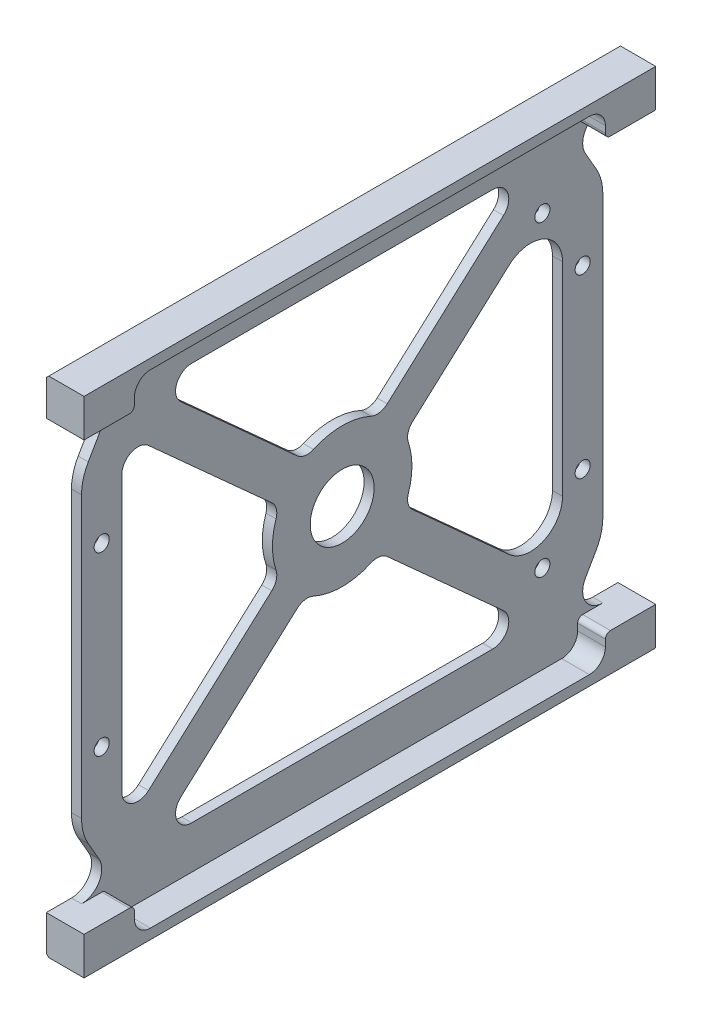
SolidWorks part; units mm, degrees
material "6061-T6 (SS)"
ref_plane "Front Plane" through (0, 0, 0) normal (0, 0, 1) x (1, 0, 0)
ref_plane "Top Plane" through (0, 0, 0) normal (0, 1, 0) x (1, 0, 0)
ref_plane "Right Plane" through (0, 0, 0) normal (1, 0, 0) x (0, 0, -1)
sketch "Sketch1" plane through (0, 0, 0) normal (0, 0, 1) x (1, 0, 0)
  line L0 (0, 50) -> (0, -50)
  line L1 (0, -50) -> (7.5, -50)
  line L2 (7.5, -50) -> (7.5, -42.5)
  line L3 (7.5, -42.5) -> (2, -42.5)
  line L4 (2, -42.5) -> (2, 42.5)
  line L5 (2, 42.5) -> (7.5, 42.5)
  line L6 (7.5, 42.5) -> (7.5, 50)
  line L7 (7.5, 50) -> (0, 50)
  dimension "D1" = 2
  dimension "D2" = 7.5
  dimension "D3" = 7.5
  dimension "D4" = 100
  dimension "D5" = 50
extrude "Boss-Extrude1" add sketch "Sketch1" along normal mid plane 113.5
sketch "Sketch2" plane through (2, 0, 0) normal (1, 0, 0) x (0, 0, -1)
  line L0 (-56.75, -42.5) -> (56.75, -42.5) construction
  line L1 (-56.75, 42.5) -> (-51.75, 42.5)
  line L2 (-56.75, 42.5) -> (-56.75, -42.5)
  line L3 (-56.75, -42.5) -> (-51.75, -42.5)
  line L4 (-51.75, 42.5) -> (-51.75, -42.5)
  line L5 (-56.75, 42.5) -> (-51.75, -42.5) construction
  line L6 (-56.75, -42.5) -> (-51.75, 42.5) construction
  line L7 (-56.75, -42.5) -> (56.75, -42.5) construction
  line L8 (56.75, 42.5) -> (51.75, 42.5)
  line L9 (56.75, 42.5) -> (56.75, -42.5)
  line L10 (56.75, -42.5) -> (51.75, -42.5)
  line L11 (51.75, 42.5) -> (51.75, -42.5)
  line L12 (56.75, 42.5) -> (51.75, -42.5) construction
  line L13 (56.75, -42.5) -> (51.75, 42.5) construction
  line L14 (47.75, 42.5) -> (47.75, -42.5) construction
  line L15 (-56.75, 42.5) -> (56.75, 42.5) construction
  line L16 (-47.75, 42.5) -> (-47.75, -42.5) construction
  line L17 (-56.75, 42.5) -> (56.75, 42.5) construction
  circle A0 centre (-47.75, 17.5) radius 1.5
  circle A1 centre (-47.75, -17.5) radius 1.5
  circle A2 centre (47.75, 17.5) radius 1.5
  circle A3 centre (47.75, -17.5) radius 1.5
  point P4 (-54.25, 0)
  point P12 (54.25, 0)
  line M1 (56.75, -42.5) -> (56.75, 42.5)
  line M2 (56.75, 42.5) -> (-56.75, 42.5)
  line M3 (-56.75, 42.5) -> (-56.75, -42.5)
  line M4 (-56.75, -42.5) -> (56.75, -42.5)
  dimension "D3" = 3
  dimension "D1" = 5
  dimension "D2" = 5
  dimension "D4" = 35
  dimension "D5" = 35
  dimension "D6" = 85
  dimension "D7" = 25
  dimension "D8" = 25
  dimension "D9" = 4
  dimension "D10" = 4
extrude "Cut-Extrude1" cut sketch "Sketch2" against normal blind 2 contours L4 M2 M3 M4 | L11 M2 M4 M1 | L14 A2 | L14 A2 | L14 A3 | L14 A3 | L16 A1 | L16 A1 | L16 A0 | L16 A0
sketch "Sketch3" plane through (2, 0, 0) normal (1, 0, 0) x (0, 0, -1)
  line L1 (-29.8997, -39.5) -> (29.8997, -39.5)
  line L2 (-43.75, -27.3035) -> (-43.75, 27.3035)
  line L3 (-29.8997, 39.5) -> (29.8997, 39.5)
  line L4 (43.75, -20.1594) -> (43.75, 20.1594)
  line L5 (-43.75, -39.5) -> (43.75, 39.5) construction
  line L6 (-43.75, 39.5) -> (34.7864, -31.4072) construction
  line L7 (-32.0273, 33.9684) -> (-8.9464, 13.1296)
  line L8 (-38.4473, 29.6602) -> (-13.9724, 7.5628)
  line L9 (32.0273, 33.9684) -> (8.9464, 13.1296)
  line L10 (33.1446, 24.8726) -> (13.9724, 7.5628)
  line L11 (-51.75, 42.5) -> (-51.75, -42.5)
  line L12 (-51.75, -42.5) -> (51.75, -42.5)
  line L13 (51.75, -42.5) -> (51.75, 42.5)
  line L14 (51.75, 42.5) -> (-51.75, 42.5)
  line L15 (-51.75, 42.5) -> (-51.75, -42.5) construction
  line L16 (-51.75, -42.5) -> (51.75, -42.5) construction
  line L17 (51.75, -42.5) -> (51.75, 42.5) construction
  line L18 (51.75, 42.5) -> (-51.75, 42.5) construction
  line L19 (33.1446, -24.8726) -> (13.9724, -7.5628)
  line L20 (32.0273, -33.9684) -> (8.9464, -13.1296)
  line L21 (-32.0273, -33.9684) -> (-8.9464, -13.1296)
  line L22 (-38.4473, -29.6602) -> (-13.9724, -7.5628)
  line L23 (51.75, -42.5) -> (56.75, -42.5) construction
  line L24 (-43.75, 39.5) -> (13.3825, 39.5) construction
  line L25 (-43.75, 39.5) -> (-43.75, -39.5) construction
  line L26 (-43.75, -39.5) -> (13.3825, -39.5) construction
  line L27 (43.75, 39.5) -> (43.75, -39.5) construction
  line L28 (32.1175, -39.5) -> (43.75, -39.5) construction
  line L30 (32.1175, 39.5) -> (43.75, 39.5) construction
  line L31 (39.75, 30.5) -> (39.75, -30.5) construction
  arc A0 (13.9724, 7.5628) -> (13.1372, 4.386) centre (15.9828, 5.3361) ccw
  circle A1 centre (47.75, 17.5) radius 1.5 construction
  arc A2 (13.1372, -4.386) -> (13.9724, -7.5628) centre (15.9828, -5.3361) ccw
  circle A3 centre (0, 0) radius 6.35
  arc A4 (-13.1372, 4.386) -> (-13.1372, -4.386) centre (0, 0) ccw
  arc A5 (5.7011, 12.6222) -> (-5.7011, 12.6222) centre (0, 0) ccw
  arc A6 (13.1372, -4.386) -> (13.1372, 4.386) centre (0, 0) ccw
  arc A7 (-5.7011, -12.6222) -> (5.7011, -12.6222) centre (0, 0) ccw
  circle A8 centre (-47.75, -17.5) radius 1.5 construction
  arc A9 (8.9464, -13.1296) -> (5.7011, -12.6222) centre (6.9359, -15.3563) ccw
  arc A10 (-5.7011, -12.6222) -> (-8.9464, -13.1296) centre (-6.9359, -15.3563) ccw
  arc A11 (-13.1372, -4.386) -> (-13.9724, -7.5628) centre (-15.9828, -5.3361) cw
  arc A12 (-13.1372, 4.386) -> (-13.9724, 7.5628) centre (-15.9828, 5.3361) ccw
  arc A13 (8.9464, 13.1296) -> (5.7011, 12.6222) centre (6.9359, 15.3563) cw
  arc A14 (-5.7011, 12.6222) -> (-8.9464, 13.1296) centre (-6.9359, 15.3563) cw
  arc A16 (43.75, 20.1594) -> (33.1446, 24.8726) centre (37.4, 20.1594) ccw
  arc A17 (43.75, -20.1594) -> (33.1446, -24.8726) centre (37.4, -20.1594) cw
  arc A19 (-29.8997, -39.5) -> (-32.0273, -33.9684) centre (-29.8997, -36.325) cw
  arc A20 (-38.4473, -29.6602) -> (-43.75, -27.3035) centre (-40.575, -27.3035) cw
  arc A21 (-43.75, 27.3035) -> (-38.4473, 29.6602) centre (-40.575, 27.3035) cw
  arc A22 (-29.8997, 39.5) -> (-32.0273, 33.9684) centre (-29.8997, 36.325) ccw
  arc A35 (29.8997, -39.5) -> (32.0273, -33.9684) centre (29.8997, -36.325) ccw
  arc A36 (32.0273, 33.9684) -> (29.8997, 39.5) centre (29.8997, 36.325) ccw
  circle A37 centre (39.75, 30.5) radius 1.5
  circle A38 centre (39.75, -30.5) radius 1.5
  point P0 (0, 0)
  point P40 (12.409, -6.1513)
  point P45 (-7.383, -11.7181)
  point P52 (7.383, 11.7181)
  dimension "D7" = 12.7
  dimension "D11" = 3
  dimension "D12" = 3.175
  dimension "D13" = 6.35
  dimension "D14" = 3.175
  dimension "D15" = 3
  dimension "D3" = 4
  dimension "D6" = 4
  dimension "D8" = 7.5
  dimension "D9" = 7.5
  dimension "D10" = 7.5
  dimension "D4" = 4
  dimension "D5" = 3
  dimension "D16" = 4
  dimension "D17" = 61
  dimension "D18" = 30.5
extrude "Cut-Extrude2" cut sketch "Sketch3" against normal through all
chamfer "Chamfer1" distance 0.5 angle 45 2 edges at (0, 50, 0) (0, -50, 0)
sketch "Sketch4" plane through (7.5, 0, 0) normal (1, 0, 0) x (0, 0, -1)
  line L5 (-56.75, -42.5) -> (56.75, -42.5) construction
  line L6 (-56.75, 42.5) -> (56.75, 42.5) construction
  line L7 (-51.75, -42.5) -> (51.75, -42.5) construction
  line L12 (-46.75, 43.5) -> (-46.75, 44.825)
  line L13 (-43.575, 48) -> (43.575, 48)
  line L14 (-56.75, -42.5) -> (-47.75, -42.5)
  line L15 (-56.75, 42.5) -> (-47.75, 42.5)
  line L16 (46.75, 44.825) -> (46.75, 43.5)
  line L17 (46.75, -43.5) -> (46.75, -44.825)
  line L18 (43.575, -48) -> (-43.575, -48)
  line L19 (-46.75, -44.825) -> (-46.75, -43.5)
  line L20 (-56.75, 50) -> (56.75, 50) construction
  line L21 (-56.75, -50) -> (56.75, -50) construction
  line L22 (47.75, 42.5) -> (56.75, 42.5)
  line L23 (47.75, -42.5) -> (56.75, -42.5)
  line L24 (-47.75, 42.5) -> (47.75, 42.5)
  line L25 (47.75, -42.5) -> (-47.75, -42.5)
  arc A0 (47.75, 42.5) -> (46.75, 43.5) centre (47.75, 43.5) cw
  arc A1 (-46.75, 43.5) -> (-47.75, 42.5) centre (-47.75, 43.5) cw
  arc A2 (47.75, -42.5) -> (46.75, -43.5) centre (47.75, -43.5) ccw
  arc A3 (-46.75, -43.5) -> (-47.75, -42.5) centre (-47.75, -43.5) ccw
  arc A4 (-43.575, -48) -> (-46.75, -44.825) centre (-43.575, -44.825) cw
  arc A5 (43.575, -48) -> (46.75, -44.825) centre (43.575, -44.825) ccw
  arc A6 (46.75, 44.825) -> (43.575, 48) centre (43.575, 44.825) ccw
  arc A7 (-43.575, 48) -> (-46.75, 44.825) centre (-43.575, 44.825) ccw
  point P24 (46.75, 42.5)
  point P27 (-46.75, 42.5)
  point P30 (46.75, -42.5)
  point P33 (-46.75, -42.5)
  line M16 (-56.75, 42.5) -> (56.75, 42.5)
  dimension "D12" = 3.175
  dimension "D11" = 1
  dimension "D6" = 5
  dimension "D7" = 5
  dimension "D8" = 5
  dimension "D9" = 2
  dimension "D10" = 2
extrude "Cut-Extrude3" cut sketch "Sketch4" against normal up to surface (5.5 mm away) contours L18 A5 L17 A2 L25 A3 L19 A4 | L13 A7 L12 A1 A0 L16 A6 M16 up to face at (2, 0, 27.4889)
sketch "Sketch5" plane through (0, 0, 0) normal (-1, 0, 0) x (0, 0, 1)
  line L0 (-56.75, 42.5) -> (-51.75, 42.5) construction
  line L5 (-50.4103, 32.8205) -> (-48.2859, 36.5)
  line L6 (-51.75, 42.5) -> (-51.75, -42.5) construction
  line L17 (-51.75, 42.5) -> (-51.75, 23.7514)
  line L19 (-51.75, -42.5) -> (-56.75, -42.5) construction
  line L25 (-48.2859, -36.5) -> (-50.4103, -32.8205)
  line L27 (-51.75, -23.3339) -> (-51.75, -42.5)
  line L30 (-51.75, 27.8205) -> (-51.75, -27.8205)
  arc A0 (-51.75, -42.5) -> (-48.2859, -36.5) centre (-51.75, -38.5) ccw
  arc A1 (-48.2859, 36.5) -> (-51.75, 42.5) centre (-51.75, 38.5) ccw
  arc A4 (-50.4103, -32.8205) -> (-51.75, -27.8205) centre (-41.75, -27.8205) cw
  arc A5 (-50.4103, 32.8205) -> (-51.75, 27.8205) centre (-41.75, 27.8205) ccw
  dimension "D2" = 4
  dimension "D5" = 30
  dimension "D6" = 10
  dimension "D1" = 30
extrude "Cut-Extrude4" cut sketch "Sketch5" against normal blind 10
mirror "Mirror1" about plane through (0, 0, 0) normal (0, 0, 1) of "Cut-Extrude4"
fillet "Fillet1" [suppressed] radius 6.35
equation "\"D3@Sketch1\"=\"D2@Sketch1\""
equation "\"D5@Sketch1\"=\"D4@Sketch1\"/2"
equation "\"D5@Sketch2\"=\"D4@Sketch2\""
equation "\"D7@Sketch2\"=(\"D6@Sketch2\"-\"D4@Sketch2\")/2"
equation "\"D8@Sketch2\"=\"D7@Sketch2\""
equation "\"D10@Sketch2\"=\"D9@Sketch2\""
equation "\"D6@Sketch3\"=\"D4@Sketch3\""
equation "\"D9@Sketch3\"=\"D8@Sketch3\""
equation "\"D10@Sketch3\"=\"D8@Sketch3\""
equation "\"D4@Sketch3\"=\"D3@Sketch3\""
equation "\"D6@Sketch4\"=\"D5@Sketch4\""
equation "\"D7@Sketch4\"=\"D5@Sketch4\""
equation "\"D8@Sketch4\"=\"D7@Sketch4\""
equation "\"D10@Sketch4\"=\"D9@Sketch4\""
equation "\"D18@Sketch3\"=\"D17@Sketch3\"/2"
equation "\"D12@Sketch3\"=\"D14@Sketch3\""
